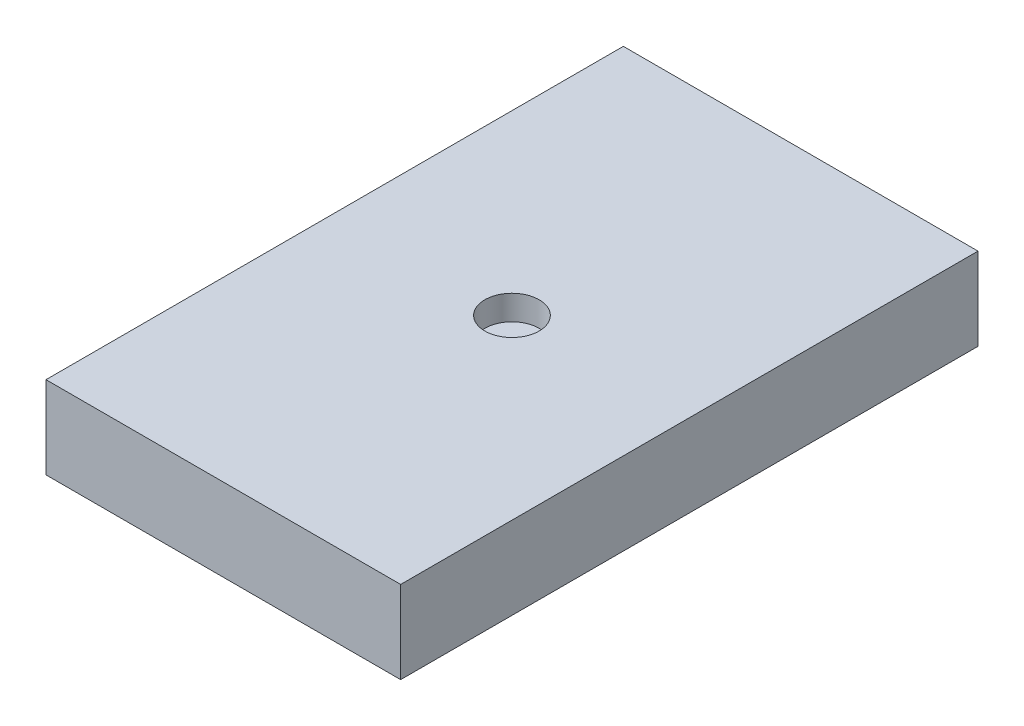
SolidWorks part; units mm, degrees
ref_plane "Front Plane" through (0, 0, 0) normal (0, 0, 1) x (1, 0, 0)
ref_plane "Top Plane" through (0, 0, 0) normal (0, 1, 0) x (1, 0, 0)
ref_plane "Right Plane" through (0, 0, 0) normal (1, 0, 0) x (0, 0, -1)
sketch "Sketch1" plane through (0, 0, 0) normal (0, 1, 0) x (1, 0, 0)
  line L1 (-5.461, -8.89) -> (5.461, -8.89)
  line L2 (-5.461, -8.89) -> (-5.461, 8.89)
  line L3 (-5.461, 8.89) -> (5.461, 8.89)
  line L4 (5.461, -8.89) -> (5.461, 8.89)
  line L5 (-5.461, -8.89) -> (5.461, 8.89) construction
  line L6 (-5.461, 8.89) -> (5.461, -8.89) construction
  point P0 (0, 0)
  dimension "D1" = 10.922
  dimension "D2" = 17.78
extrude "Boss-Extrude1" add sketch "Sketch1" along normal blind 2.54
sketch "Sketch2" plane through (0, 2.54, 0) normal (0, 1, 0) x (1, 0, 0)
  circle A0 centre (0, 0) radius 0.8358
extrude "Cut-Extrude1" cut sketch "Sketch2" against normal blind 0.762
